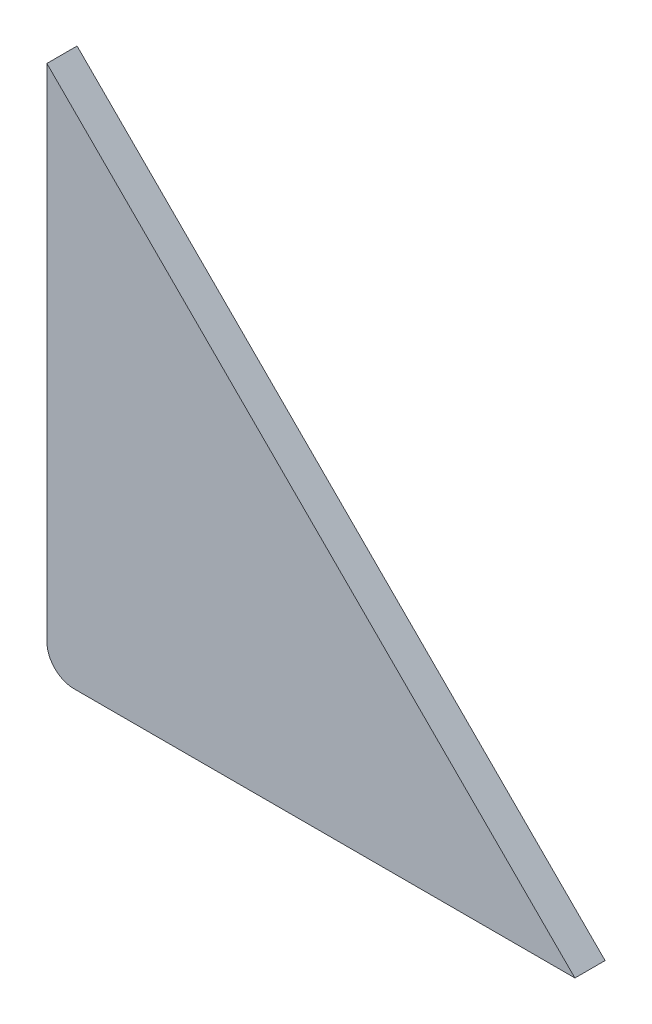
SolidWorks part; units mm, degrees
ref_plane "Front Plane" through (0, 0, 0) normal (0, 0, 1) x (1, 0, 0)
ref_plane "Top Plane" through (0, 0, 0) normal (0, 1, 0) x (1, 0, 0)
ref_plane "Right Plane" through (0, 0, 0) normal (1, 0, 0) x (0, 0, -1)
sketch "Sketch1" plane through (0, 0, 0) normal (0, 0, 1) x (1, 0, 0)
  line L0 (0, 1.8) -> (0, 35)
  line L1 (0, 35) -> (35, 0)
  line L2 (35, 0) -> (1.8, 0)
  arc A0 (0, 1.8) -> (1.8, 0) centre (1.8, 1.8) ccw
  point P6 (0, 0)
  dimension "D3" = 1.8
  dimension "D1" = 35
  dimension "D2" = 35
extrude "Boss-Extrude1" add sketch "Sketch1" along normal blind 2
